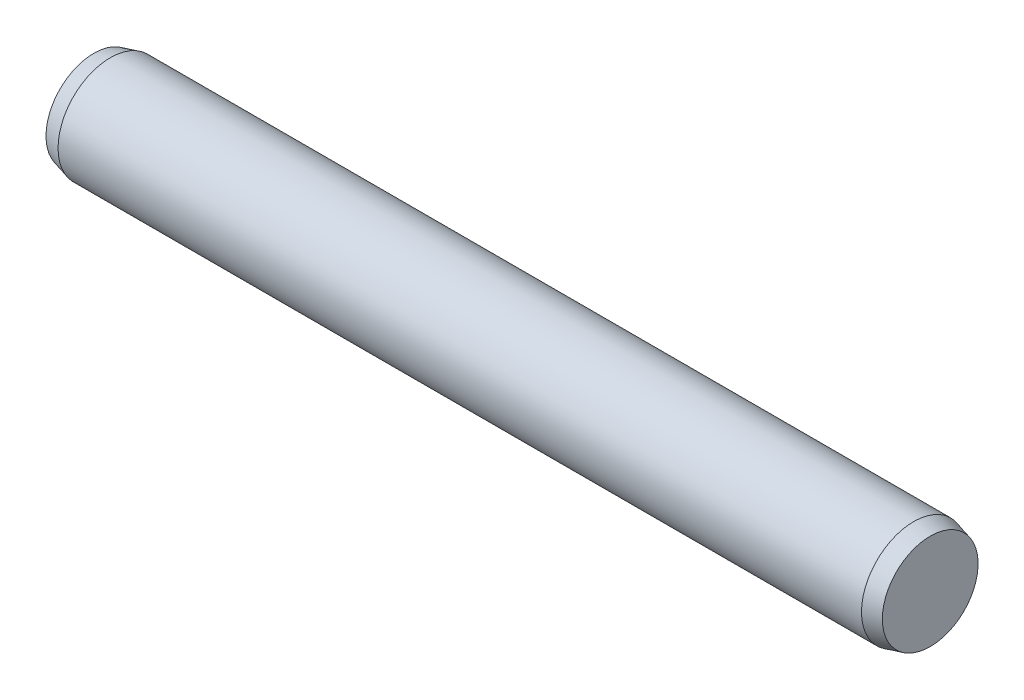
SolidWorks part; units mm, degrees
ref_plane "Plane1" through (0, 0, 0) normal (0, 0, 1) x (1, 0, 0)
ref_plane "Plane2" through (0, 0, 0) normal (0, 1, 0) x (1, 0, 0)
ref_plane "Plane3" through (0, 0, 0) normal (1, 0, 0) x (0, 0, -1)
sketch "Sketch1" plane through (0, 0, 0) normal (0, 0, 1) x (1, 0, 0)
  line L1 (-6.35, 0) -> (107.95, 0) construction
  line L2 (0, 0) -> (32, 0)
  line L3 (32, 0) -> (32, 1.8312)
  line L4 (32, 1.8312) -> (31.37, 2)
  line L5 (31.37, 2) -> (0.63, 2)
  line L6 (0, 1.8312) -> (0, 0)
  line L7 (0, 1.8312) -> (0.63, 2)
  dimension "Chamfer_len" = 0.63
  dimension "D3" = 15
  dimension "Diameter" = 4
  dimension "D1" = 0.63
  dimension "D2" = 15
  dimension "Length" = 32
revolve "Base-Revolve" add sketch "Sketch1" angle 360 about L1
equation "\"D3@Sketch1\" = 15.0"
equation "\"D1@Sketch1\" = \"Chamfer_len@Sketch1\""
equation "\"D2@Sketch1\" = \"D3@Sketch1\""
